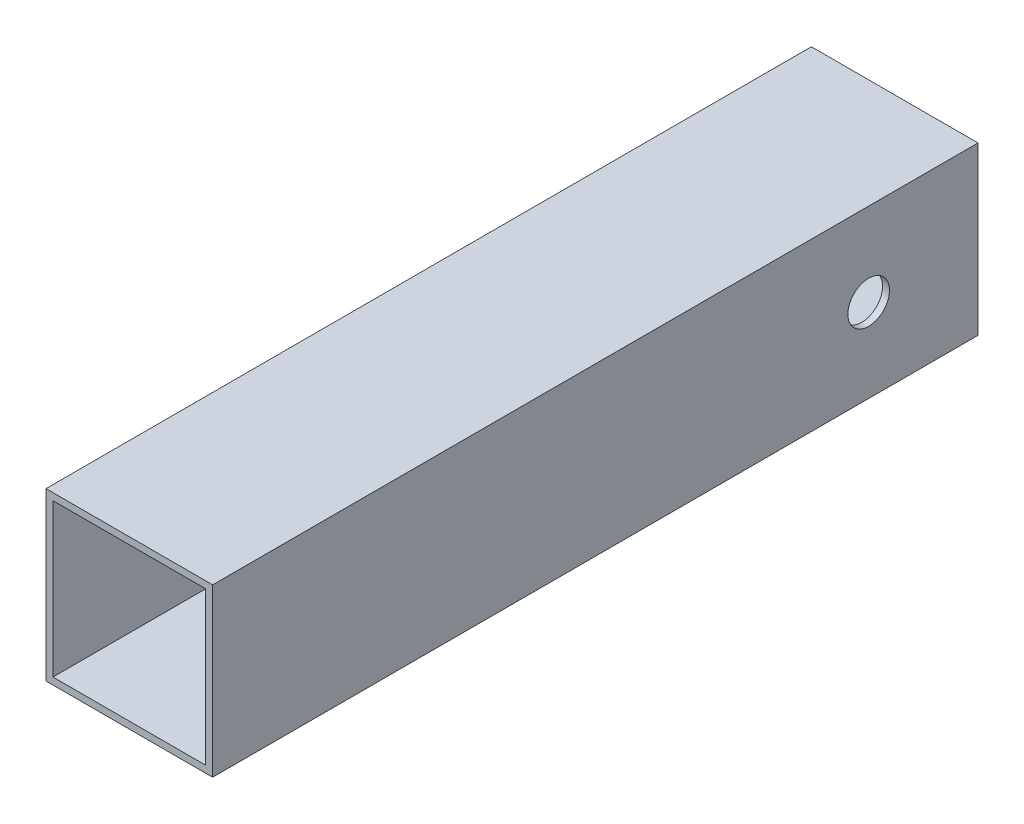
SolidWorks part; units mm, degrees
ref_plane "Alzado" through (0, 0, 0) normal (0, 0, 1) x (1, 0, 0)
ref_plane "Planta" through (0, 0, 0) normal (0, 1, 0) x (1, 0, 0)
ref_plane "Vista lateral" through (0, 0, 0) normal (1, 0, 0) x (0, 0, -1)
sketch "Croquis1" plane through (0, 0, 0) normal (0, 0, 1) x (1, 0, 0)
  line L0 (3.175, -3.175) -> (73.025, -3.175)
  line L1 (0, 0) -> (76.2, 0)
  line L2 (0, 0) -> (0, -76.2)
  line L3 (0, -76.2) -> (76.2, -76.2)
  line L4 (76.2, 0) -> (76.2, -76.2)
  line L5 (73.025, -3.175) -> (73.025, -73.025)
  line L6 (3.175, -73.025) -> (73.025, -73.025)
  line L7 (3.175, -3.175) -> (3.175, -73.025)
  dimension "D1" = 76.2
  dimension "D2" = 76.2
  dimension "D3" = 3.175
extrude "Saliente-Extruir1" add sketch "Croquis1" along normal blind 350
sketch "Croquis3" plane through (0, 0, 0) normal (-1, 0, 0) x (0, 0, 1)
  line L0 (0, -38.1) -> (50, -38.1) construction
  line L1 (0, 0) -> (0, -76.2) construction
  circle A0 centre (50, -38.1) radius 9.525
  dimension "D2" = 19.05
  dimension "D1" = 50
extrude "Cortar-Extruir2" cut sketch "Croquis3" against normal blind 127
